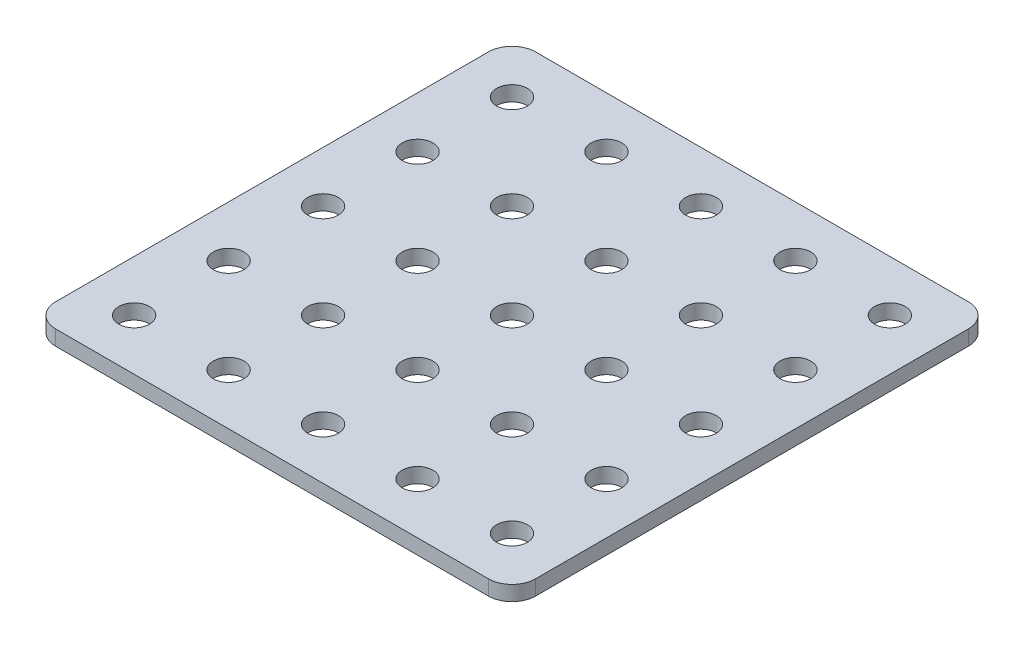
SolidWorks part; units mm, degrees
material "6061 Alloy"
ref_plane "Front Plane" through (0, 0, 0) normal (0, 0, 1) x (1, 0, 0)
ref_plane "Top Plane" through (0, 0, 0) normal (0, 1, 0) x (1, 0, 0)
ref_plane "Right Plane" through (0, 0, 0) normal (1, 0, 0) x (0, 0, -1)
sketch "Sketch1" plane through (0, 0, 0) normal (0, 1, 0) x (1, 0, 0)
  line L1 (-50.8, 50.8) -> (50.8, 50.8)
  line L2 (-50.8, 50.8) -> (-50.8, -50.8)
  line L3 (-50.8, -50.8) -> (50.8, -50.8)
  line L4 (50.8, 50.8) -> (50.8, -50.8)
  line L5 (-50.8, 50.8) -> (50.8, -50.8) construction
  line L6 (-50.8, -50.8) -> (50.8, 50.8) construction
  point P0 (0, 0)
  dimension "D1" = 101.6
  dimension "D2" = 101.6
extrude "Boss-Extrude1" add sketch "Sketch1" along normal blind 3.175
fillet "Fillet1" radius 5 4 edges at (50.8, 1.5875, -50.8) (-50.8, 1.5875, -50.8) (-50.8, 1.5875, 50.8) (50.8, 1.5875, 50.8)
sketch "Sketch2" plane through (0, 3.175, 0) normal (0, 1, 0) x (1, 0, 0)
  line L0 (0, 0) -> (20, 0) construction
  line L1 (20, 0) -> (40, 0) construction
  line L3 (0, -15.9401) -> (0, 0) construction
  line L4 (0, 0) -> (-20, 0) construction
  line L5 (-20, 0) -> (-40, 0) construction
  circle A0 centre (0, 0) radius 3.25
  circle A1 centre (20, 0) radius 3.25
  circle A2 centre (40, 0) radius 3.25
  circle A3 centre (-20, 0) radius 3.25
  circle A4 centre (-40, 0) radius 3.25
  dimension "D1" = 6.5
  dimension "D2" = 20
extrude "Cut-Extrude1" cut sketch "Sketch2" against normal blind 3.175
pattern_linear "LPattern1" count 3 spacing 20 along (0, 0, 1) of "Cut-Extrude1"
pattern_linear "LPattern2" count 3 spacing 20 along (0, 0, -1) of "Cut-Extrude1"
